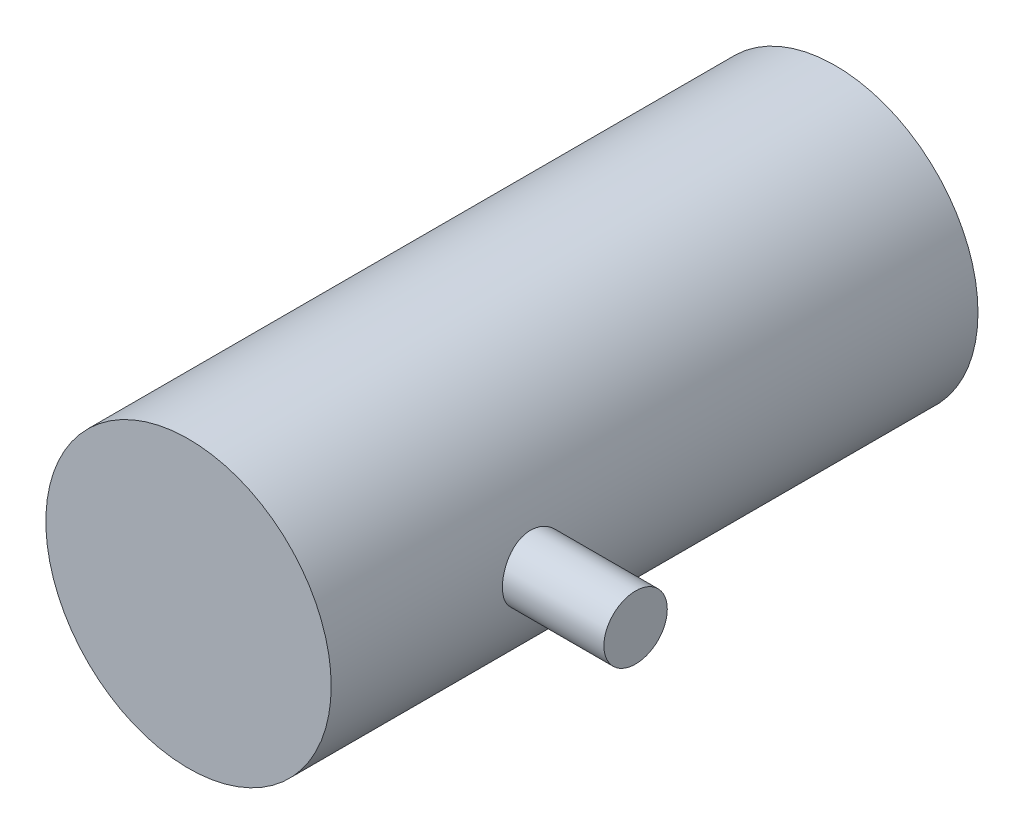
SolidWorks part; units mm, degrees
ref_plane "Alzado" through (0, 0, 0) normal (0, 0, 1) x (1, 0, 0)
ref_plane "Planta" through (0, 0, 0) normal (0, 1, 0) x (1, 0, 0)
ref_plane "Vista lateral" through (0, 0, 0) normal (1, 0, 0) x (0, 0, -1)
sketch "Croquis1" plane through (0, 0, 0) normal (0, 0, 1) x (1, 0, 0)
  circle A0 centre (0, 0) radius 225
  dimension "D1" = 450
extrude "Saliente-Extruir1" add sketch "Croquis1" along normal blind 1020
sketch "Croquis2" plane through (0, 0, 0) normal (1, 0, 0) x (0, 0, -1)
  line L0 (-1020, 225) -> (-1020, -225) construction
  line L1 (-1020, 0) -> (0, 0) construction
  circle A0 centre (-700, 0) radius 50
  dimension "D1" = 100
  dimension "D2" = 320
extrude "Saliente-Extruir2" add sketch "Croquis2" along normal blind 385
